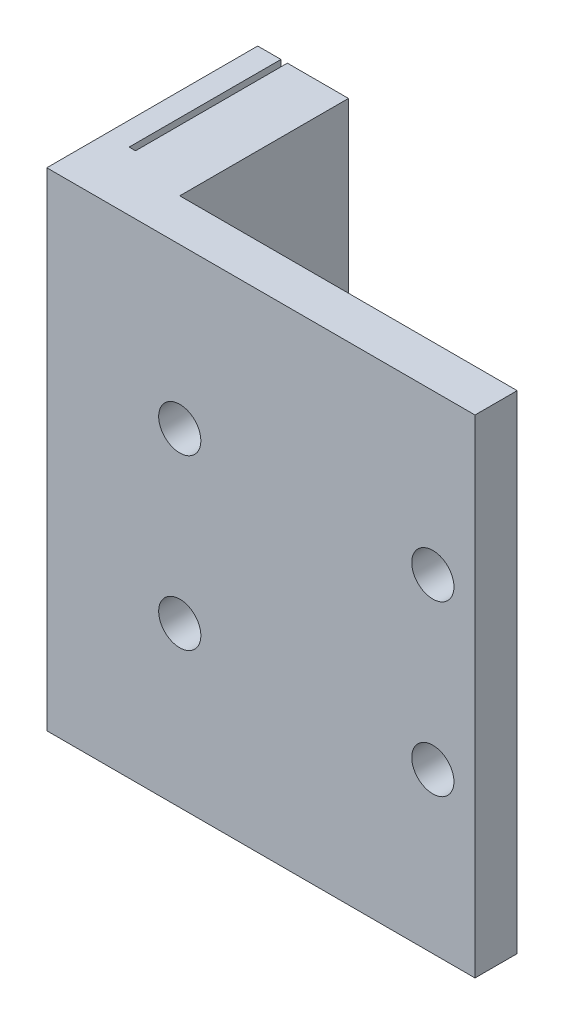
SolidWorks part; units mm, degrees
ref_plane "Front Plane" through (0, 0, 0) normal (0, 0, 1) x (1, 0, 0)
ref_plane "Top Plane" through (0, 0, 0) normal (0, 1, 0) x (1, 0, 0)
ref_plane "Right Plane" through (0, 0, 0) normal (1, 0, 0) x (0, 0, -1)
sketch "Sketch1" plane through (0, 0, 0) normal (0, 0, 1) x (1, 0, 0)
  line L0 (9.79, -14.45) -> (-8.7959, -14.45) construction
  line L1 (-10, -9.45) -> (-10, 9.45) construction
  line L2 (10, 9.45) -> (10, -9.45) construction
  line L3 (-9.79, 14.45) -> (8.7959, 14.45) construction
  line L4 (9.79, -14.45) -> (-8.7959, -14.45)
  line L5 (-10, -14.45) -> (-10, 14.45)
  line L6 (10, 14.45) -> (10, -14.45)
  line L7 (-9.79, 14.45) -> (8.7959, 14.45)
  line L8 (-9.79, 14.45) -> (-10, 14.45)
  line L9 (8.7959, 14.45) -> (10, 14.45)
  line L10 (-8.7959, -14.45) -> (-10, -14.45)
  line L11 (9.79, -14.45) -> (10, -14.45)
  circle A0 centre (-7.5, -5) radius 1.25 construction
  circle A1 centre (-7.5, 5) radius 1.25 construction
  circle A2 centre (7.5, 5) radius 1.25 construction
  circle A3 centre (7.5, -5) radius 1.25 construction
  circle A4 centre (-7.5, -5) radius 1.25
  circle A5 centre (-7.5, 5) radius 1.25
  circle A6 centre (7.5, 5) radius 1.25
  circle A7 centre (7.5, -5) radius 1.25
  dimension "D1" = 15
  dimension "D2" = 10
extrude "Boss-Extrude1" add sketch "Sketch1" along normal blind 2.5 contours A5 | A4 | A6 | A7 | L5 L8 L7 L9 L6 L11 L4 L10
ref_plane "Plane1" through (0, 0, 0) normal (-1, 0, 0) x (0, 0, 1)
sketch "Sketch3" plane through (-10, 0, 0) normal (-1, 0, 0) x (0, 0, 1)
  line L1 (2.5, -14.45) -> (-10, -14.45)
  line L2 (2.5, -14.45) -> (2.5, 14.45)
  line L3 (2.5, 14.45) -> (-10, 14.45)
  line L4 (-10, -14.45) -> (-10, 14.45)
  dimension "D1" = 12.5
extrude "Boss-Extrude2" add sketch "Sketch3" along normal blind 5.38
sketch "Sketch4" plane through (0, 0, -10) normal (0, 0, -1) x (-1, 0, 0)
  line L0 (13.6213, 14.1948) -> (13.6213, 14.4475)
  line L1 (13.6213, 14.4475) -> (14.3833, 14.4475)
  line L2 (13.6213, 12.1948) -> (13.6213, 12.7003)
  line L3 (13.6213, 10.1948) -> (13.6213, 10.7003)
  line L4 (13.6213, 8.1948) -> (13.6213, 8.7003)
  line L5 (13.6213, 4.4475) -> (13.6213, 4.7003)
  line L6 (13.6213, 6.1948) -> (13.6213, 6.7003)
  line L7 (14.3833, 14.4475) -> (14.3833, 4.4475)
  line L9 (14.3833, 4.4475) -> (13.6213, 4.4475)
  line L10 (14.0023, 4.4475) -> (14.0023, 14.4475) construction
  arc A0 (13.6213, 12.7003) -> (13.4907, 12.8489) centre (13.4714, 12.7003) ccw
  arc A1 (13.0818, 12.9955) -> (13.4907, 12.8489) centre (13.6213, 13.8565) ccw
  arc A2 (13.0818, 13.8995) -> (13.0818, 12.9955) centre (13.4232, 13.4475) ccw
  arc A3 (13.4907, 14.0462) -> (13.0818, 13.8995) centre (13.6213, 13.0386) ccw
  arc A4 (13.4907, 14.0462) -> (13.6213, 14.1948) centre (13.4714, 14.1948) ccw
  arc A5 (13.6213, 10.7003) -> (13.4907, 10.8489) centre (13.4714, 10.7003) ccw
  arc A6 (13.0818, 10.9955) -> (13.4907, 10.8489) centre (13.6213, 11.8565) ccw
  arc A7 (13.0818, 11.8995) -> (13.0818, 10.9955) centre (13.4232, 11.4475) ccw
  arc A8 (13.4907, 12.0462) -> (13.0818, 11.8995) centre (13.6213, 11.0386) ccw
  arc A9 (13.4907, 12.0462) -> (13.6213, 12.1948) centre (13.4714, 12.1948) ccw
  arc A10 (13.6213, 8.7003) -> (13.4907, 8.8489) centre (13.4714, 8.7003) ccw
  arc A11 (13.0818, 8.9955) -> (13.4907, 8.8489) centre (13.6213, 9.8565) ccw
  arc A12 (13.0818, 9.8995) -> (13.0818, 8.9955) centre (13.4232, 9.4475) ccw
  arc A13 (13.4907, 10.0462) -> (13.0818, 9.8995) centre (13.6213, 9.0386) ccw
  arc A14 (13.4907, 10.0462) -> (13.6213, 10.1948) centre (13.4714, 10.1948) ccw
  arc A15 (13.6213, 6.7003) -> (13.4907, 6.8489) centre (13.4714, 6.7003) ccw
  arc A16 (13.0818, 6.9955) -> (13.4907, 6.8489) centre (13.6213, 7.8565) ccw
  arc A17 (13.0818, 7.8995) -> (13.0818, 6.9955) centre (13.4232, 7.4475) ccw
  arc A18 (13.4907, 8.0461) -> (13.0818, 7.8995) centre (13.6213, 7.0386) ccw
  arc A19 (13.4907, 8.0461) -> (13.6213, 8.1948) centre (13.4714, 8.1948) ccw
  arc A20 (13.6213, 4.7003) -> (13.4907, 4.8489) centre (13.4714, 4.7003) ccw
  arc A21 (13.0818, 4.9955) -> (13.4907, 4.8489) centre (13.6213, 5.8565) ccw
  arc A22 (13.0818, 5.8995) -> (13.0818, 4.9955) centre (13.4232, 5.4475) ccw
  arc A23 (13.4907, 6.0461) -> (13.0818, 5.8995) centre (13.6213, 5.0386) ccw
  arc A24 (13.4907, 6.0461) -> (13.6213, 6.1948) centre (13.4714, 6.1948) ccw
extrude "Cut-Extrude1" cut sketch "Sketch4" against normal blind 9
pattern_linear "LPattern1" count 4 spacing 10 along (0, -1, 0) count 2 spacing 10 along (0, 1, 0) of "Cut-Extrude1"
mirror "Mirror1" [suppressed] about plane through (0, 0, 0) normal (-1, 0, 0)
